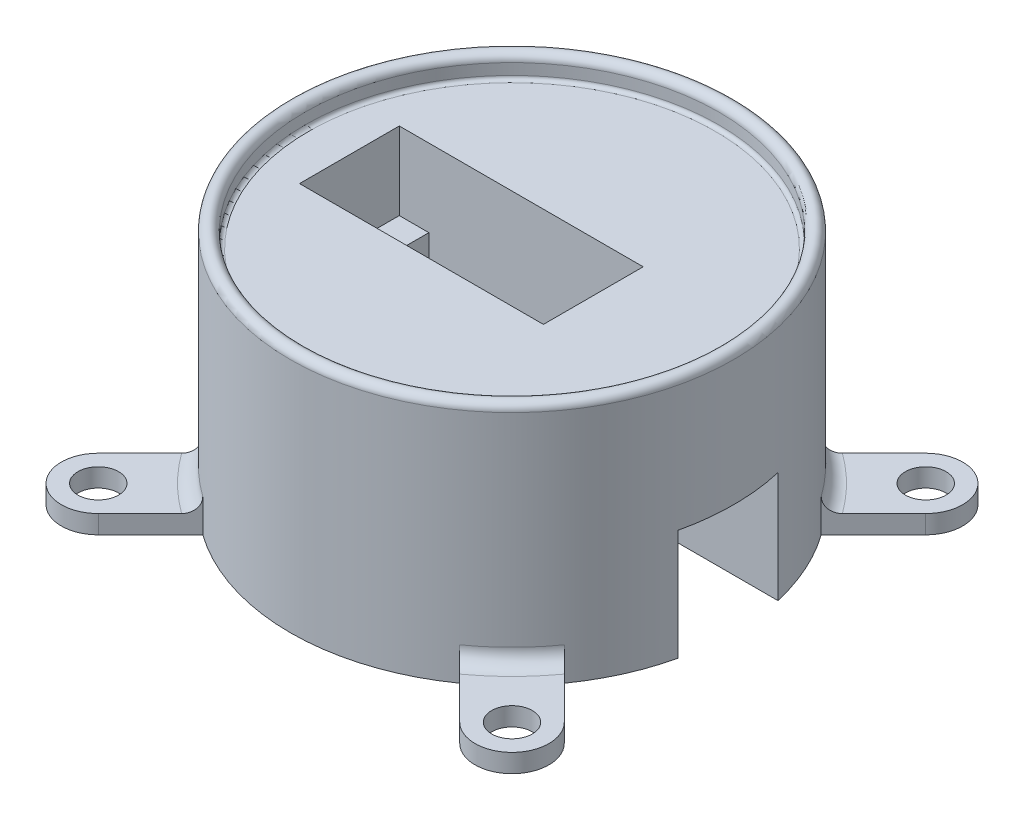
SolidWorks part; units mm, degrees
material "PVC 0.007 Plasticized"
ref_plane "Front Plane" through (0, 0, 0) normal (0, 0, 1) x (1, 0, 0)
ref_plane "Top Plane" through (0, 0, 0) normal (0, 1, 0) x (1, 0, 0)
ref_plane "Right Plane" through (0, 0, 0) normal (1, 0, 0) x (0, 0, -1)
sketch "Sketch2" plane through (0, 0, 0) normal (0, 1, 0) x (1, 0, 0)
  circle A0 centre (0, 0) radius 30
  dimension "D1" = 60
extrude "Boss-Extrude1" add sketch "Sketch2" along normal blind 30
sketch "Sketch3" plane through (0, 0, 0) normal (1, 0, 0) x (0, 0, -1)
  line L0 (-30, 0) -> (30, 0) construction
  line L1 (-6.75, 0) -> (6.75, 0)
  line L2 (-6.75, 0) -> (-6.75, 15)
  line L3 (-6.75, 15) -> (6.75, 15)
  line L4 (6.75, 0) -> (6.75, 15)
  point P6 (0, 0)
  dimension "D1" = 13.5
  dimension "D2" = 15
extrude "Cut-Extrude1" cut sketch "Sketch3" along normal through all
sketch "Sketch4" plane through (0, 30, 0) normal (0, 1, 0) x (1, 0, 0)
  line L0 (0, 6.75) -> (0, -6.75) construction
  line L1 (-22, 6.75) -> (11, 6.75)
  line L2 (-22, 6.75) -> (-22, -6.75)
  line L3 (-22, -6.75) -> (11, -6.75)
  line L4 (11, 6.75) -> (11, -6.75)
  point P6 (0, 0)
  dimension "D1" = 33
  dimension "D2" = 13.5
  dimension "D3" = 11
extrude "Cut-Extrude2" cut sketch "Sketch4" against normal blind 10.5
sketch "Sketch5" plane through (0, 19.5, 0) normal (0, 1, 0) x (1, 0, 0)
  line L0 (11, 6.75) -> (-22, 6.75) construction
  line L1 (-18, 6.75) -> (7, 6.75)
  line L2 (-18, 6.75) -> (-18, -6.75)
  line L3 (-18, -6.75) -> (7, -6.75)
  line L4 (7, 6.75) -> (7, -6.75)
  line L5 (-22, -6.75) -> (11, -6.75) construction
  line L6 (-5.5, 6.75) -> (-5.5, -6.75) construction
  line L7 (11, 6.75) -> (-22, 6.75) construction
  line L8 (-22, -6.75) -> (11, -6.75) construction
  point P14 (-5.5, -6.75)
  dimension "D1" = 25
extrude "Cut-Extrude3" cut sketch "Sketch5" against normal through all
sketch "Sketch7" plane through (0, 0, 0) normal (0, 0, 1) x (1, 0, 0)
  line L0 (0, 34.9598) -> (0, -3.5827) construction
  line L1 (30, 30) -> (28, 30)
  line L2 (30, 30) -> (30, 32)
  line L4 (28, 30) -> (28, 32)
  arc A0 (28, 32) -> (30, 32) centre (29, 32) cw
  dimension "D1" = 2
  dimension "D2" = 2
revolve "Revolve1" add sketch "Sketch7" angle 360 about L0
fillet "Fillet1" radius 0.5 1 edges at (0, 30, 28)
sketch "Sketch8" plane through (0, 0, 0) normal (0, 1, 0) x (1, 0, 0)
  line L0 (37.7964, 37.7964) -> (-37.7964, -37.7964) construction
  line L1 (-37.7964, 37.7964) -> (37.7964, -37.7964) construction
  line L2 (24.452, 17.381) -> (31.5231, 24.452)
  line L3 (17.3665, 24.4375) -> (24.452, 31.5231)
  line L4 (17.381, -24.452) -> (24.452, -31.5231)
  line L5 (24.4375, -17.3665) -> (31.5231, -24.452)
  line L6 (-24.452, -17.381) -> (-31.5231, -24.452)
  line L7 (-17.3665, -24.4375) -> (-24.452, -31.5231)
  line L8 (-17.381, 24.452) -> (-24.452, 31.5231)
  line L9 (-24.4375, 17.3665) -> (-31.5231, 24.452)
  arc A0 (24.452, 31.5231) -> (31.5231, 24.452) centre (27.9876, 27.9876) cw
  circle A1 centre (0, 0) radius 30 construction
  arc A3 (24.452, 17.381) -> (17.381, 24.452) centre (0, 0) ccw
  arc A4 (17.381, -24.452) -> (24.452, -17.381) centre (0, 0) ccw
  arc A5 (31.5231, -24.452) -> (24.452, -31.5231) centre (27.9876, -27.9876) cw
  arc A6 (-24.452, -17.381) -> (-17.381, -24.452) centre (0, 0) ccw
  arc A7 (-24.452, -31.5231) -> (-31.5231, -24.452) centre (-27.9876, -27.9876) cw
  arc A8 (-17.381, 24.452) -> (-24.452, 17.381) centre (0, 0) ccw
  arc A9 (-31.5231, 24.452) -> (-24.452, 31.5231) centre (-27.9876, 27.9876) cw
  point P4 (0, 0)
  point P5 (0, 0)
  dimension "D2" = 5
  dimension "D1" = 10
  dimension "D3" = 4
extrude "Boss-Extrude2" add sketch "Sketch8" along normal blind 2.5 contours A5 L5 A4 L4 | A7 L7 A6 L6 | A3 L2 A0 L3 | A9 L9 A8 L8
sketch "Sketch9" plane through (0, 2.5, 0) normal (0, 1, 0) x (1, 0, 0)
  line L0 (-37.3789, 37.3789) -> (37.3789, -37.3789) construction
  line L1 (-37.3789, -37.3789) -> (37.3789, 37.3789) construction
  circle A0 centre (-27.9876, 27.9876) radius 2.75
  circle A1 centre (27.9876, 27.9876) radius 2.75
  circle A2 centre (27.9876, -27.9876) radius 2.75
  circle A3 centre (-27.9876, -27.9876) radius 2.75
  point P4 (0, 0)
  point P5 (0, 0)
  dimension "D1" = 5.5
  dimension "D2" = 4
extrude "Cut-Extrude4" cut sketch "Sketch9" against normal through all
sketch "Sketch10" plane through (0, 19.5, 0) normal (0, 1, 0) x (1, 0, 0)
  line L1 (-22, 6.75) -> (-22, -6.75) construction
  line L3 (-5.5, 6.75) -> (-5.5, -6.75) construction
  line L4 (11, 6.75) -> (-22, 6.75) construction
  line L5 (-22, -6.75) -> (11, -6.75) construction
  circle A0 centre (-20, 0) radius 1.5
  circle A1 centre (9, 0) radius 1.5
  dimension "D1" = 3
  dimension "D2" = 2
extrude "Cut-Extrude5" cut sketch "Sketch10" against normal blind 5
fillet "Fillet2" radius 2 4 edges at (-21.2132, 2.5, -21.2132) (21.2132, 2.5, -21.2132) (21.2132, 2.5, 21.2132) (-21.2132, 2.5, 21.2132)
